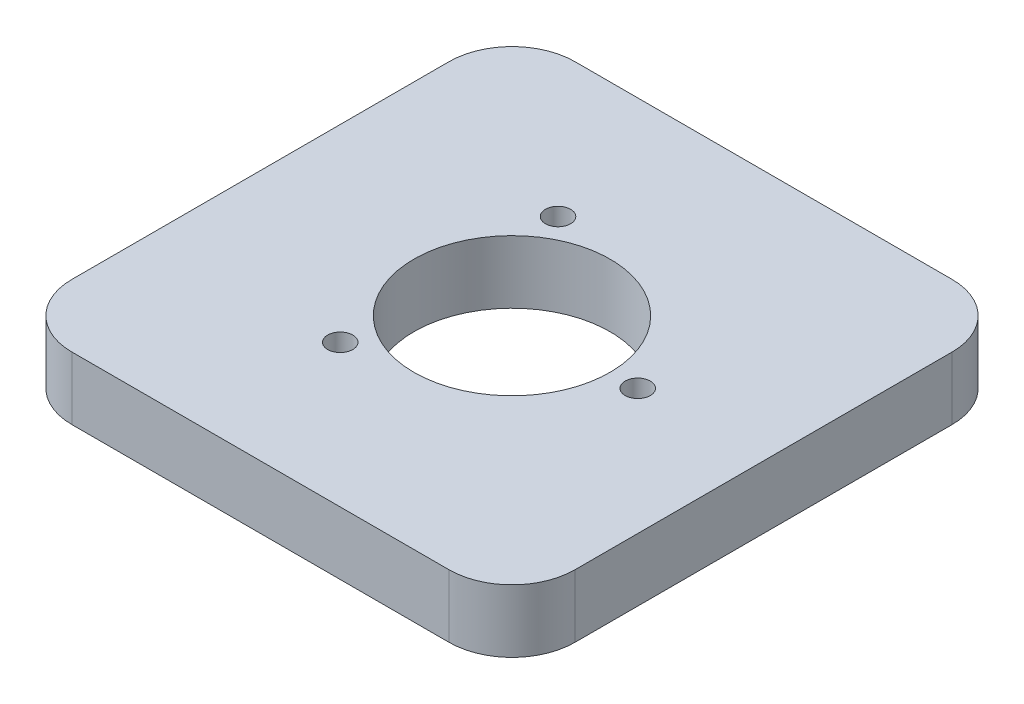
SolidWorks part; units mm, degrees
ref_plane "Front Plane" through (0, 0, 0) normal (0, 0, 1) x (1, 0, 0)
ref_plane "Top Plane" through (0, 0, 0) normal (0, 1, 0) x (1, 0, 0)
ref_plane "Right Plane" through (0, 0, 0) normal (1, 0, 0) x (0, 0, -1)
sketch "Sketch1" plane through (0, 0, 0) normal (0, 1, 0) x (1, 0, 0)
  line L1 (-25.4, -25.4) -> (25.4, -25.4)
  line L2 (-25.4, -25.4) -> (-25.4, 25.4)
  line L3 (-25.4, 25.4) -> (25.4, 25.4)
  line L4 (25.4, -25.4) -> (25.4, 25.4)
  line L5 (-25.4, -25.4) -> (25.4, 25.4) construction
  line L6 (-25.4, 25.4) -> (25.4, -25.4) construction
  point P0 (0, 0)
  dimension "D1" = 50.8
  dimension "D2" = 50.8
extrude "Boss-Extrude1" add sketch "Sketch1" along normal blind 6.35
sketch "Sketch2" plane through (0, 6.35, 0) normal (0, 1, 0) x (1, 0, 0)
  circle A0 centre (0, 0) radius 9.906
  dimension "D1" = 19.812
extrude "Cut-Extrude1" cut sketch "Sketch2" against normal through all
sketch "Sketch3" plane through (0, 6.35, 0) normal (0, 1, 0) x (1, 0, 0)
  line L0 (0, 0) -> (12.7, 0) construction
  circle A0 centre (12.7, 0) radius 1.27
  dimension "D2" = 2.54
  dimension "D1" = 12.7
extrude "Cut-Extrude2" cut sketch "Sketch3" against normal through all
pattern_circular "CirPattern1" count 3 over 360 about axis through (0, 0, 0) along (0, 1, 0) of "Cut-Extrude2"
fillet "Fillet1" radius 6.35 4 edges at (25.4, 3.175, 25.4) (-25.4, 3.175, 25.4) (25.4, 3.175, -25.4) (-25.4, 3.175, -25.4)
